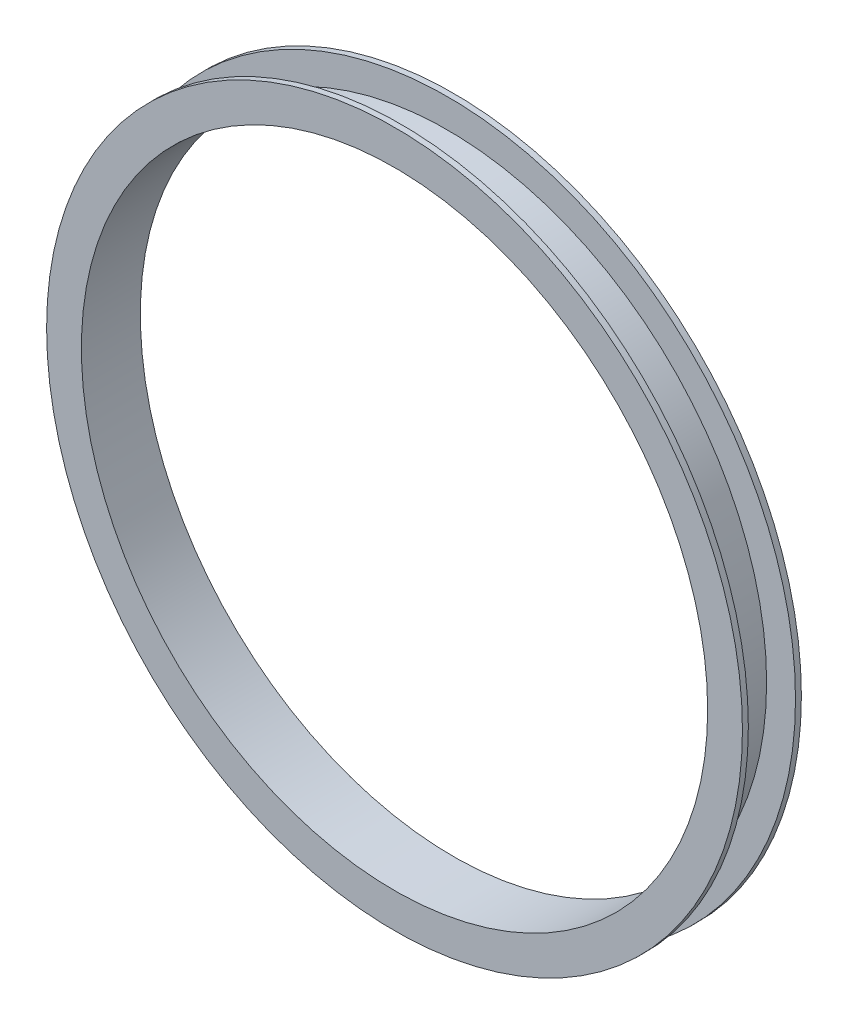
SolidWorks part; units mm, degrees
material "Maple"
ref_plane "Wasteboard" through (0, 0, 0) normal (0, 0, 1) x (1, 0, 0)
ref_plane "Left-Right" through (0, 0, 0) normal (0, 1, 0) x (1, 0, 0)
ref_plane "Front-Back" through (0, 0, 0) normal (1, 0, 0) x (0, 0, -1)
sketch "Sketch2" plane through (0, 0, 0) normal (0, 0, 1) x (1, 0, 0)
  circle A0 centre (0, 0) radius 192.0875 construction
  circle A1 centre (0, 0) radius 209.55 construction
  circle A2 centre (0, 0) radius 171.831 construction
  circle A3 centre (0, 0) radius 252.73 construction
  circle A4 centre (0, 0) radius 184.531 construction
  circle A5 centre (0, 0) radius 187.3885
  circle A6 centre (0, 0) radius 168.656
  dimension "D1" = 384.175
  dimension "D2" = 419.1
  dimension "D3" = 343.662
  dimension "D4" = 505.46
  dimension "D5" = 369.062
  dimension "D6" = 374.777
  dimension "D7" = 337.312
extrude "Boss-Extrude1" add sketch "Sketch2" along normal blind 3.175
sketch "Sketch3" plane through (0, 0, 3.175) normal (0, 0, 1) x (1, 0, 0)
  circle A0 centre (0, 0) radius 171.831
  circle A1 centre (0, 0) radius 168.656
  dimension "D1" = 343.662
extrude "Boss-Extrude2" add sketch "Sketch3" along normal blind 25.4
sketch "Sketch4" plane through (0, 0, 28.575) normal (0, 0, 1) x (1, 0, 0)
  circle A0 centre (0, 0) radius 187.3885
  circle A1 centre (0, 0) radius 168.656
extrude "Boss-Extrude3" add sketch "Sketch4" along normal blind 3.175
sketch "Sketch7" plane through (0, 0, 0) normal (0, 0, 1) x (1, 0, 0)
  line L0 (0, 0) -> (-204.984, 0)
  line L1 (0, 0) -> (-194.9514, 63.3435)
  line L2 (0, 0) -> (-165.8355, 120.4866)
  line L3 (0, 0) -> (-120.4866, 165.8355)
  line L4 (0, 0) -> (-63.3435, 194.9514)
  line L5 (0, 0) -> (0, 204.984)
  line L6 (0, 0) -> (63.3435, 194.9514)
  line L7 (0, 0) -> (120.4866, 165.8355)
  line L8 (0, 0) -> (165.8355, 120.4866)
  line L9 (0, 0) -> (194.9514, 63.3435)
  line L10 (0, 0) -> (204.984, 0)
  line L11 (0, 0) -> (194.9514, -63.3435)
  line L12 (0, 0) -> (165.8355, -120.4866)
  line L13 (0, 0) -> (120.4866, -165.8355)
  line L14 (0, 0) -> (63.3435, -194.9514)
  line L15 (0, 0) -> (0, -204.984)
  line L16 (0, 0) -> (-63.3435, -194.9514)
  line L17 (0, 0) -> (-120.4866, -165.8355)
  line L18 (0, 0) -> (-165.8355, -120.4866)
  line L19 (0, 0) -> (-194.9514, -63.3435)
  point P24 (0, 0)
  dimension "D1" = 20
